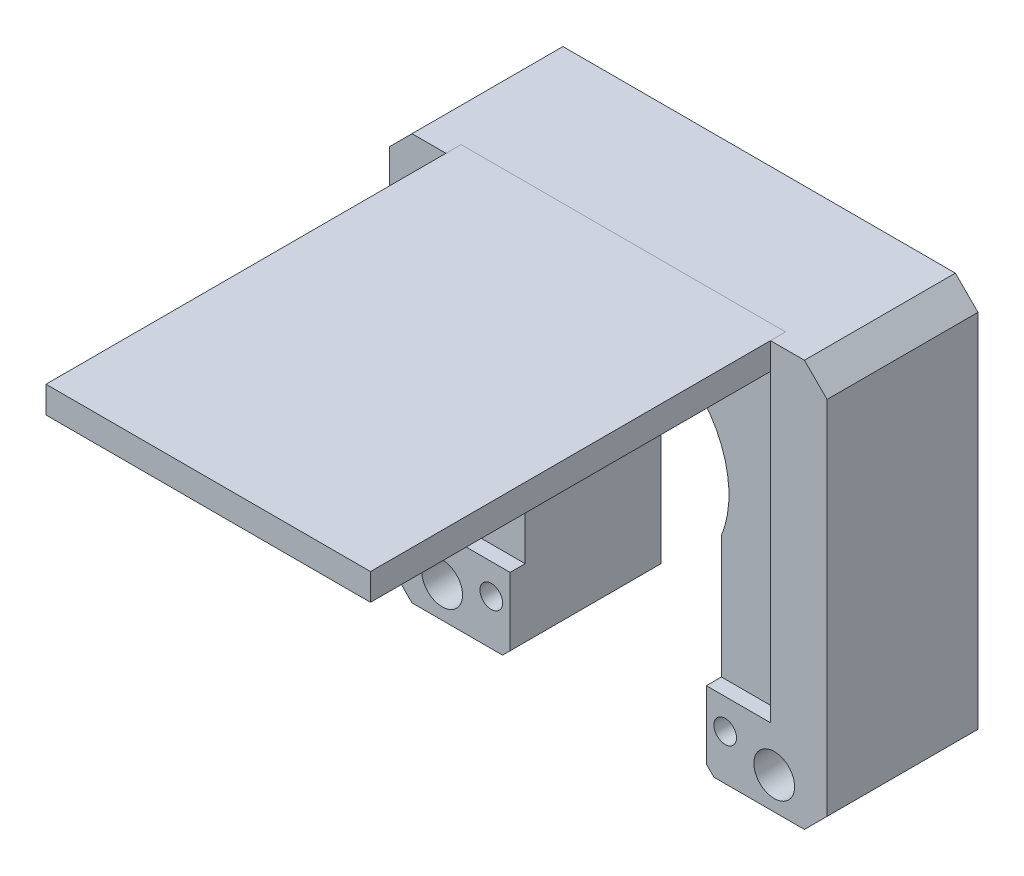
SolidWorks part; units mm, degrees
ref_plane "Front Plane" through (0, 0, 0) normal (0, 0, 1) x (1, 0, 0)
ref_plane "Top Plane" through (0, 0, 0) normal (0, 1, 0) x (1, 0, 0)
ref_plane "Right Plane" through (0, 0, 0) normal (1, 0, 0) x (0, 0, -1)
sketch "Sketch1" plane through (0, 0, 0) normal (0, 0, 1) x (1, 0, 0)
  line L0 (0, 0) -> (0, 36.8169) construction
  line L1 (-24.2051, 0) -> (24.2051, 0) construction
  line L2 (29, 10) -> (-29, 10)
  line L3 (-29, 10) -> (-29, 0)
  line L4 (-29, 0) -> (-29, -43.8477)
  line L5 (-29, -43.8477) -> (29, -43.8477)
  line L6 (0, 0) -> (0, -53.7245) construction
  line L7 (29, 10) -> (29, 0)
  line L8 (29, 0) -> (29, -43.8477)
  circle A1 centre (0, -12.4297) radius 14
  point P6 (0, 0)
  point P15 (0, -43.8477)
  point P16 (0, 10)
  dimension "D1" = 28
  dimension "D2" = 10
  dimension "D4" = 29
extrude "Boss-Extrude1" add sketch "Sketch1" along normal blind 20
sketch "Sketch3" plane through (0, 0, 0) normal (0, 0, -1) x (-1, 0, 0)
  line L0 (0, 0) -> (0, -43.5497) construction
  line L1 (0, -39.5977) -> (-22, -39.5977) construction
  line L2 (29, -43.8477) -> (-29, -43.8477) construction
  circle A0 centre (-22, -39.5977) radius 2.7
  circle A1 centre (22, -39.5977) radius 2.7
  dimension "D1" = 5.4
  dimension "D2" = 22
  dimension "D3" = 4.25
extrude "Cut-Extrude2" cut sketch "Sketch3" against normal up to next
sketch "Sketch4" plane through (0, 0, 0) normal (0, 0, -1) x (-1, 0, 0)
  circle A0 centre (-22, -39.5977) radius 4.3
  circle A1 centre (22, -39.5977) radius 4.3
  dimension "D1" = 8.6
extrude "Cut-Extrude3" cut sketch "Sketch4" against normal blind 3
chamfer "Chamfer1" distance 3 angle 45 4 edges at (29, 10, 10) (-29, 10, 10) (-29, -43.8477, 10) (29, -43.8477, 10)
sketch "Sketch5" plane through (0, 0, 20) normal (0, 0, 1) x (1, 0, 0)
  line L0 (0, -39.5089) -> (0, 39.5089) construction
  line L1 (0, 25.0792) -> (-21.5, 10)
  line L2 (26, 10) -> (-26, 10) construction
  line L3 (-21.5, 10) -> (-21.5, -33.8477)
  line L4 (-21.5, -33.8477) -> (21.5, -33.8477)
  line L5 (-26, -43.8477) -> (26, -43.8477) construction
  line L6 (0, 25.0792) -> (21.5, 10)
  line L7 (21.5, 10) -> (21.5, -33.8477)
  point P4 (0, 0)
  point P14 (0, -33.8477)
  dimension "D1" = 21.5
  dimension "D2" = 10
extrude "Cut-Extrude4" cut sketch "Sketch5" against normal blind 2
sketch "Sketch6" plane through (0, 0, 20) normal (0, 0, 1) x (1, 0, 0)
  line L0 (0, 0) -> (0, -44.8711) construction
  line L1 (-26, -43.8477) -> (26, -43.8477) construction
  line L2 (-13, -69.9993) -> (13, -69.9993)
  line L3 (-13, -69.9993) -> (-13, -17.6961)
  line L4 (-13, -17.6961) -> (13, -17.6961)
  line L5 (13, -69.9993) -> (13, -17.6961)
  line L6 (-13, -69.9993) -> (13, -17.6961) construction
  line L7 (-13, -17.6961) -> (13, -69.9993) construction
  point P3 (0, -43.8477)
  dimension "D1" = 26
extrude "Cut-Extrude5" cut sketch "Sketch6" against normal up to next
chamfer "Chamfer2" distance 1 angle 45 2 edges at (-13, -43.8477, 10) (13, -43.8477, 10)
sketch "Sketch9" plane through (0, 0, 18) normal (0, 0, 1) x (1, 0, 0)
  line L0 (-21.5, 10) -> (21.5, 10)
  line L6 (-21.5, 10) -> (-21.5, 6.466)
  line L7 (-21.5, 10) -> (-21.5, -33.8477) construction
  line L8 (-21.5, 6.466) -> (21.5, 6.466)
  line L9 (21.5, -33.8477) -> (21.5, 10) construction
  line L10 (21.5, 6.466) -> (21.5, 10)
extrude "Boss-Extrude2" add sketch "Sketch9" along normal blind 55 separate body
sketch "Sketch10" plane through (0, 0, 20) normal (0, 0, 1) x (1, 0, 0)
  line L0 (0, 0) -> (0, -63.4398) construction
  line L1 (-26, -43.8477) -> (-14, -43.8477) construction
  circle A0 centre (-15.5, -37.8477) radius 1.5
  circle A1 centre (15.5, -37.8477) radius 1.5
  dimension "D1" = 3
  dimension "D2" = 15.5
  dimension "D3" = 6
extrude "Cut-Extrude6" cut sketch "Sketch10" against normal through all
